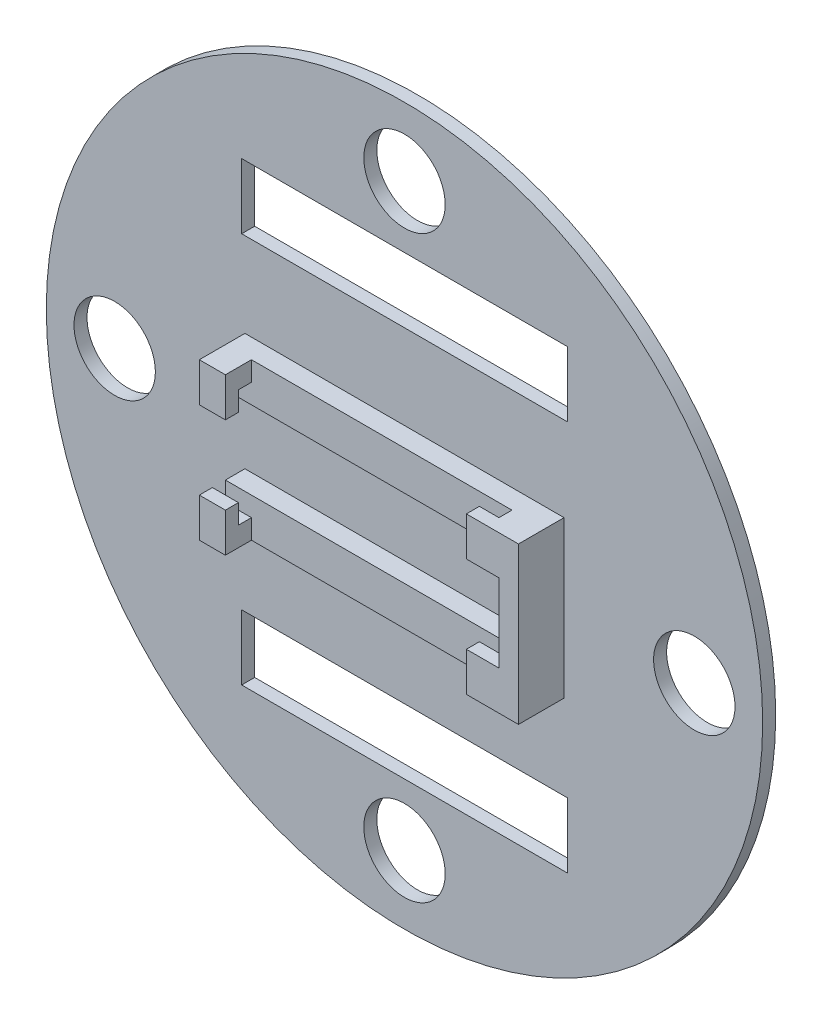
SolidWorks part; units mm, degrees
ref_plane "Front Plane" through (0, 0, 0) normal (0, 0, 1) x (1, 0, 0)
ref_plane "Top Plane" through (0, 0, 0) normal (0, 1, 0) x (1, 0, 0)
ref_plane "Right Plane" through (0, 0, 0) normal (1, 0, 0) x (0, 0, -1)
sketch "Sketch4" plane through (0, 0, 0) normal (0, 0, 1) x (1, 0, 0)
  circle A0 centre (0, 0) radius 59
  dimension "D1" = 118
extrude "Boss-Extrude3" add sketch "Sketch4" along normal blind 2
sketch "Sketch5" plane through (0, 0, 2) normal (0, 0, 1) x (1, 0, 0)
  line L1 (-22.5, 27.5) -> (22.5, 27.5)
  line L2 (-22.5, 27.5) -> (-22.5, -27.5)
  line L3 (-22.5, -27.5) -> (22.5, -27.5)
  line L4 (22.5, 27.5) -> (22.5, -27.5)
  circle A0 centre (0, 0) radius 59 construction
  circle A1 centre (-22.5, 27.5) radius 1.375
  circle A2 centre (22.5, 27.5) radius 1.375
  circle A3 centre (22.5, -27.5) radius 1.375
  circle A4 centre (-22.5, -27.5) radius 1.375
  dimension "D5" = 2.75
  dimension "D6" = 2.75
  dimension "D7" = 2.75
  dimension "D8" = 2.75
  dimension "D1" = 45
  dimension "D2" = 55
  dimension "D3" = 27.5
  dimension "D4" = 22.5
extrude "Boss-Extrude5" add sketch "Sketch5" along normal blind 7 contours A4 | A3 | A2 | A1
sketch "Sketch8" plane through (0, 0, 2) normal (0, 0, 1) x (1, 0, 0)
  circle A4 centre (-22.5, 27.5) radius 2.375
  circle A5 centre (-22.5, 27.5) radius 2.375
  circle A7 centre (22.5, 27.5) radius 2.375
  circle A8 centre (22.5, 27.5) radius 2.375
  circle A10 centre (-22.5, -27.5) radius 2.375
  circle A11 centre (-22.5, -27.5) radius 2.375
  circle A13 centre (22.5, -27.5) radius 2.375
  circle A14 centre (22.5, -27.5) radius 2.375
  dimension "D1" = 1
  dimension "D2" = 1
  dimension "D3" = 1
  dimension "D4" = 1
extrude "Boss-Extrude6" add sketch "Sketch8" along normal blind 2
sketch "Sketch9" plane through (0, 0, 2) normal (0, 0, 1) x (1, 0, 0)
  line L0 (4.7458, 55.7985) -> (5, 58.7878)
  line L1 (55.7985, -4.7458) -> (58.7878, -5)
  line L2 (-4.7458, 55.7985) -> (-5, 58.7878)
  line L3 (55.7985, 4.7458) -> (58.7878, 5)
  line L4 (-4.7458, -55.7985) -> (-5, -58.7878)
  line L5 (4.7458, -55.7985) -> (5, -58.7878)
  line L6 (-55.7985, 4.7458) -> (-58.7878, 5)
  line L7 (-55.7985, -4.7458) -> (-58.7878, -5)
  arc A0 (5, 58.7878) -> (-5, 58.7878) centre (0, 0) ccw
  arc A1 (5, 58.7878) -> (-5, 58.7878) centre (0, 0) ccw
  arc A2 (4.7458, 55.7985) -> (-4.7458, 55.7985) centre (0, 0) ccw
  arc A3 (55.7985, -4.7458) -> (55.7985, 4.7458) centre (0, 0) ccw
  arc A4 (58.7878, -5) -> (58.7878, 5) centre (0, 0) ccw
  arc A5 (-4.7458, -55.7985) -> (4.7458, -55.7985) centre (0, 0) ccw
  arc A6 (-5, -58.7878) -> (5, -58.7878) centre (0, 0) ccw
  arc A7 (-55.7985, 4.7458) -> (-55.7985, -4.7458) centre (0, 0) ccw
  arc A8 (-58.7878, 5) -> (-58.7878, -5) centre (0, 0) ccw
  point P25 (0, 0)
  circle M7 centre (0, 0) radius 59
  dimension "D1" = 118
  dimension "D2" = 3
  dimension "D3" = 4
extrude "Boss-Extrude7" add sketch "Sketch9" along normal blind 18 contours A2 L0 L2 M7 | A7 L6 L7 M7 | A4 L3 A3 L1 | A5 L5 A6 L4
sketch "Sketch10" plane through (0, 0, 2) normal (0, 0, 1) x (1, 0, 0)
  circle A0 centre (-40, 0) radius 7.5
  dimension "D1" = 15
  dimension "D2" = 40
extrude "Cut-Extrude1" cut sketch "Sketch10" against normal blind 18 contours A0
sketch "Sketch12" plane through (0, 0, 20) normal (0, 0, 1) x (1, 0, 0)
  circle A0 centre (0, 0) radius 57.5
  arc A1 (4.7458, 55.7985) -> (-4.7458, 55.7985) centre (0, 0) ccw construction
  dimension "D1" = 1.5
extrude "Cut-Extrude2" cut sketch "Sketch12" against normal blind 5
sketch "Sketch13" plane through (0, 0, 0) normal (0, 0, -1) x (-1, 0, 0)
  line L0 (-58.6183, 6.9928) -> (-53.5993, 6.5659)
  line L1 (-53.5993, -6.5659) -> (-58.6183, -6.9928)
  line L2 (6.9928, 58.6183) -> (6.5659, 53.5993)
  line L3 (-6.5659, 53.5993) -> (-6.9928, 58.6183)
  line L4 (58.6183, -6.9928) -> (53.5993, -6.5659)
  line L5 (53.5993, 6.5659) -> (58.6183, 6.9928)
  line L6 (-6.9928, -58.6183) -> (-6.5659, -53.5993)
  line L7 (6.5659, -53.5993) -> (6.9928, -58.6183)
  line L8 (5, 58.7878) -> (4.7458, 55.7985) construction
  line L9 (-4.7458, 55.7985) -> (-5, 58.7878) construction
  line L10 (55.7985, 4.7458) -> (58.7878, 5) construction
  line L11 (58.7878, -5) -> (55.7985, -4.7458) construction
  line L12 (4.7458, -55.7985) -> (5, -58.7878) construction
  line L13 (-5, -58.7878) -> (-4.7458, -55.7985) construction
  line L14 (-55.7985, -4.7458) -> (-58.7878, -5) construction
  line L15 (-58.7878, 5) -> (-55.7985, 4.7458) construction
  line L16 (4.7458, -55.7985) -> (5, -58.7878)
  line L17 (-5, -58.7878) -> (-4.7458, -55.7985)
  line L18 (-55.7985, -4.7458) -> (-58.7878, -5)
  line L19 (-58.7878, 5) -> (-55.7985, 4.7458)
  line L20 (-4.7458, 55.7985) -> (-5, 58.7878)
  line L21 (5, 58.7878) -> (4.7458, 55.7985)
  line L22 (55.7985, 4.7458) -> (58.7878, 5)
  line L23 (58.7878, -5) -> (55.7985, -4.7458)
  line L24 (4.8686, -57.2433) -> (5, -58.7878)
  line L25 (-5, -58.7878) -> (-4.8686, -57.2433)
  line L26 (-57.2433, -4.8686) -> (-58.7878, -5)
  line L27 (-58.7878, 5) -> (-57.2433, 4.8686)
  line L28 (-4.8686, 57.2433) -> (-5, 58.7878)
  line L29 (5, 58.7878) -> (4.8686, 57.2433)
  line L30 (57.2433, 4.8686) -> (58.7878, 5)
  line L31 (58.7878, -5) -> (57.2433, -4.8686)
  arc A0 (4.8686, 57.2433) -> (-4.8686, 57.2433) centre (0, 0) ccw
  circle A1 centre (0, 0) radius 59
  arc A2 (58.7878, -5) -> (58.7878, 5) centre (0, 0) ccw
  arc A3 (57.2433, -4.8686) -> (57.2433, 4.8686) centre (0, 0) ccw
  arc A4 (-4.8686, -57.2433) -> (4.8686, -57.2433) centre (0, 0) ccw
  arc A5 (-53.5993, 6.5659) -> (-53.5993, -6.5659) centre (0, 0) ccw
  arc A6 (6.5659, 53.5993) -> (-6.5659, 53.5993) centre (0, 0) ccw
  arc A7 (53.5993, -6.5659) -> (53.5993, 6.5659) centre (0, 0) ccw
  arc A8 (-6.5659, -53.5993) -> (6.5659, -53.5993) centre (0, 0) ccw
  circle A9 centre (0, 0) radius 59
  arc A10 (-5, -58.7878) -> (5, -58.7878) centre (0, 0) ccw
  arc A11 (-58.7878, 5) -> (-58.7878, -5) centre (0, 0) ccw
  arc A13 (-57.2433, 4.8686) -> (-57.2433, -4.8686) centre (0, 0) ccw
  arc A18 (5, -58.7878) -> (58.7878, -5) centre (0, 0) ccw
  arc A19 (-4.7458, -55.7985) -> (4.7458, -55.7985) centre (0, 0) ccw
  arc A20 (-58.7878, -5) -> (-5, -58.7878) centre (0, 0) ccw
  arc A21 (-55.7985, 4.7458) -> (-55.7985, -4.7458) centre (0, 0) ccw
  arc A22 (-5, 58.7878) -> (-58.7878, 5) centre (0, 0) ccw
  arc A23 (4.7458, 55.7985) -> (-4.7458, 55.7985) centre (0, 0) ccw
  arc A24 (58.7878, 5) -> (5, 58.7878) centre (0, 0) ccw
  arc A25 (55.7985, -4.7458) -> (55.7985, 4.7458) centre (0, 0) ccw
  arc A34 (4.7458, 55.7985) -> (-4.7458, 55.7985) centre (0, 0) ccw construction
  arc A35 (55.7985, -4.7458) -> (55.7985, 4.7458) centre (0, 0) ccw construction
  arc A36 (-4.7458, -55.7985) -> (4.7458, -55.7985) centre (0, 0) ccw construction
  arc A37 (-55.7985, 4.7458) -> (-55.7985, -4.7458) centre (0, 0) ccw construction
  dimension "D1" = 0
  dimension "D2" = 0
  dimension "D4" = 2
  dimension "D5" = 2
extrude "Cut-Extrude3" cut sketch "Sketch13" against normal blind 5.5
sketch "Sketch14" plane through (0, 0, 2) normal (0, 0, 1) x (1, 0, 0)
  circle A0 centre (0, 0) radius 44.4281
extrude "Cut-Extrude4" cut sketch "Sketch14" along normal blind 32
sketch "Sketch15" plane through (0, 0, 2) normal (0, 0, 1) x (1, 0, 0)
  line L2 (21.5, -6) -> (21.5, 6)
  line L6 (-24.5, -12) -> (24.5, -12)
  line L7 (24.5, -12) -> (24.5, 12)
  line L8 (-24.5, 12) -> (24.5, 12)
  line L9 (-24.5, -12) -> (-24.5, -6)
  line L10 (-24.5, 6) -> (-24.5, 12)
  line L11 (-24.5, 12) -> (24.5, 12)
  line L12 (-24.5, 12) -> (-24.5, 6)
  line L13 (-24.5, 6) -> (21.5, 6)
  line L14 (24.5, 12) -> (24.5, 6)
  line L15 (24.5, -12) -> (-24.5, -12)
  line L16 (24.5, -12) -> (24.5, -6)
  line L17 (21.5, -6) -> (-24.5, -6)
  line L18 (-24.5, -12) -> (-24.5, -6)
  line L19 (-24.5, -12) -> (-24.5, 12) construction
  line L21 (-21.5, -9) -> (-21.5, 9) construction
  line L24 (21.5, -9) -> (21.5, 9) construction
  line L25 (-21.5, 9) -> (21.5, 9) construction
  line L26 (-21.5, -9) -> (21.5, -9) construction
  point P1 (0, 0)
  dimension "D4" = 6
  dimension "D5" = 6
  dimension "D3" = 3
extrude "Boss-Extrude8" add sketch "Sketch15" along normal blind 3 contours L2 L17 L9 L6 L7 L8 L10 L13
sketch "Sketch17" plane through (0, 0, 5) normal (0, 0, 1) x (1, 0, 0)
  line L1 (21.5, -9) -> (-21.5, -9)
  line L2 (21.5, -9) -> (21.5, 9)
  line L3 (21.5, 9) -> (-21.5, 9)
  line L14 (-21.5, 9) -> (-24.5, 9)
  line L15 (-24.5, 12) -> (24.5, 12)
  line L16 (-24.5, 12) -> (-24.5, 9)
  line L17 (-24.5, -12) -> (24.5, -12)
  line L18 (24.5, 12) -> (24.5, -12)
  line L19 (-21.5, -9) -> (-24.5, -9)
  line L20 (-24.5, -9) -> (-24.5, -12)
  point P0 (0, 0)
  dimension "D1" = 43
  dimension "D2" = 18
extrude "Boss-Extrude9" add sketch "Sketch17" along normal blind 2
sketch "Sketch18" plane through (0, 0, 7) normal (0, 0, 1) x (1, 0, 0)
  line L0 (24.5, 12) -> (-24.5, 12) construction
  line L1 (-20.5, 12) -> (19.5, 12)
  line L2 (-20.5, 12) -> (-20.5, -12)
  line L3 (-20.5, -12) -> (19.5, -12)
  line L4 (19.5, 12) -> (19.5, -12)
  line L5 (-24.5, -12) -> (24.5, -12) construction
  line L6 (-24.5, 12) -> (-24.5, 9) construction
  dimension "D1" = 4
  dimension "D2" = 5
extrude "Cut-Extrude5" cut sketch "Sketch18" against normal blind 2
sketch "Sketch19" plane through (0, 0, 7) normal (0, 0, 1) x (1, 0, 0)
  line L0 (-24.5, 6) -> (21.5, 6) construction
  line L1 (-24.5, 12) -> (-20.5, 12)
  line L2 (-24.5, 12) -> (-24.5, 6)
  line L3 (-24.5, 6) -> (-20.5, 6)
  line L4 (-20.5, 12) -> (-20.5, 6)
  line L5 (21.5, -6) -> (-24.5, -6) construction
  line L6 (-24.5, -12) -> (-20.5, -12)
  line L7 (-24.5, -12) -> (-24.5, -6)
  line L8 (-24.5, -6) -> (-20.5, -6)
  line L9 (-20.5, -12) -> (-20.5, -6)
  line L10 (19.5, 12) -> (-20.5, 12) construction
  line L11 (24.5, -12) -> (16.5, -12)
  line L12 (24.5, -12) -> (24.5, 12)
  line L13 (24.5, 12) -> (16.5, 12)
  line L14 (16.5, -12) -> (16.5, 12)
  dimension "D1" = 4
  dimension "D2" = 4
  dimension "D3" = 8
extrude "Boss-Extrude10" add sketch "Sketch19" along normal blind 2
sketch "Sketch20" plane through (0, 0, 2) normal (0, 0, 1) x (1, 0, 0)
  circle A0 centre (0, 0) radius 50.9724
  circle A1 centre (0, 0) radius 71.0344
extrude "Cut-Extrude6" cut sketch "Sketch20" along normal blind 57
sketch "Sketch21" plane through (0, 0, 2) normal (0, 0, 1) x (1, 0, 0)
  circle A0 centre (0, 0) radius 57
  circle A1 centre (0, 0) radius 79.1442
  dimension "D1" = 114
extrude "Cut-Extrude8" cut sketch "Sketch21" against normal blind 57
sketch "Sketch23" plane through (0, 0, 2) normal (0, 0, 1) x (1, 0, 0)
  line L0 (0, 57) -> (0, 64.4029) construction
  line L1 (-5, 57) -> (5, 57)
  line L2 (4.6313, 52.7973) -> (5, 57)
  line L3 (-4.6313, 52.7973) -> (-5, 57)
  line L4 (52.7973, 4.6313) -> (57, 5)
  line L5 (57, 5) -> (57, -5)
  line L6 (52.7973, -4.6313) -> (57, -5)
  line L7 (4.6313, -52.7973) -> (5, -57)
  line L8 (5, -57) -> (-5, -57)
  line L9 (-4.6313, -52.7973) -> (-5, -57)
  line L10 (-52.7973, -4.6313) -> (-57, -5)
  line L11 (-57, -5) -> (-57, 5)
  line L12 (-52.7973, 4.6313) -> (-57, 5)
  circle A0 centre (0, 0) radius 57
  arc A1 (4.6313, 52.7973) -> (-4.6313, 52.7973) centre (0, 0) ccw
  circle A2 centre (0, 0) radius 57
  arc A3 (52.7973, -4.6313) -> (52.7973, 4.6313) centre (0, 0) ccw
  circle A4 centre (0, 0) radius 57
  arc A5 (-4.6313, -52.7973) -> (4.6313, -52.7973) centre (0, 0) ccw
  circle A6 centre (0, 0) radius 57
  arc A7 (-52.7973, 4.6313) -> (-52.7973, -4.6313) centre (0, 0) ccw
  point P8 (0, 57)
  point P28 (0, 0)
  circle M19 centre (0, 0) radius 57
  dimension "D1" = 114
  dimension "D2" = 4
  dimension "D3" = 10
  dimension "D4" = 4
extrude "Boss-Extrude11" add sketch "Sketch23" along normal blind 22 contours A1 L2 L3 M19 | A3 L6 L4 M19 | A7 L10 L11 L12 | A5 L7 L8 L9
sketch "Sketch24" plane through (0, 0, 24) normal (0, 0, 1) x (1, 0, 0)
  circle A0 centre (0, 0) radius 57
  circle A1 centre (0, 0) radius 89.5881
  dimension "D1" = 114
extrude "Cut-Extrude12" cut sketch "Sketch24" against normal blind 75
sketch "Sketch25" plane through (0, 0, 2) normal (0, 0, 1) x (1, 0, 0)
  circle A0 centre (0, 0) radius 55
  circle A1 centre (0, 0) radius 63.0853
  dimension "D1" = 110
extrude "Cut-Extrude13" cut sketch "Sketch25" against normal blind 10
sketch "Sketch26" plane through (0, 0, 0) normal (0, 0, -1) x (-1, 0, 0)
  circle A0 centre (0, 0) radius 55
  circle A1 centre (0, 0) radius 62.7158
extrude "Cut-Extrude14" cut sketch "Sketch26" against normal blind 43
sketch "Sketch27" plane through (0, 0, 24) normal (0, 0, 1) x (1, 0, 0)
  circle A0 centre (-55, 0) radius 8.6287
  arc A1 (-54.7896, 4.8061) -> (-54.7896, -4.8061) centre (0, 0) ccw construction
  circle A2 centre (0, -55) radius 7.7712
  arc A3 (-4.8061, -54.7896) -> (4.8061, -54.7896) centre (0, 0) ccw construction
  circle A4 centre (55, 0) radius 11.5322
  arc A5 (54.7896, -4.8061) -> (54.7896, 4.8061) centre (0, 0) ccw construction
  circle A6 centre (0, 53) radius 7.0527
  arc A7 (4.6313, 52.7973) -> (-4.6313, 52.7973) centre (0, 0) ccw construction
extrude "Cut-Extrude15" cut sketch "Sketch27" against normal up to surface (22 mm away) up to face at (-0.75, 0, 2)
sketch "Sketch28" plane through (0, 0, 2) normal (0, 0, 1) x (1, 0, 0)
  circle A0 centre (0, 0) radius 55
extrude "Boss-Extrude12" add sketch "Sketch28" against normal up to surface (2 mm away) up to face at (-32.5, 0, 0)
sketch "Sketch29" plane through (0, 0, 9) normal (0, 0, 1) x (1, 0, 0)
  line L0 (16.5, 12) -> (16.5, -12) construction
  line L1 (21.5, 6) -> (16.5, 6)
  line L2 (21.5, 6) -> (21.5, -6)
  line L3 (21.5, -6) -> (16.5, -6)
  line L4 (16.5, 6) -> (16.5, -6)
  line L5 (21.5, -6) -> (-24.5, -6) construction
extrude "Cut-Extrude16" cut sketch "Sketch29" against normal blind 3
sketch "Sketch30" plane through (0, 0, 2) normal (0, 0, 1) x (1, 0, 0)
  line L0 (0, 55) -> (0, -55) construction
  line L1 (55, 0) -> (-55, 0) construction
  circle A0 centre (0, 0) radius 55 construction
  circle A1 centre (0, 0) radius 44.5
  circle A2 centre (0, 44.5) radius 6.25
  circle A3 centre (44.5, 0) radius 6.25
  circle A4 centre (0, -44.5) radius 6.25
  circle A5 centre (-44.5, 0) radius 6.25
  dimension "D1" = 10.5
  dimension "D2" = 12.5
  dimension "D3" = 12.5
  dimension "D4" = 12.5
  dimension "D5" = 12.5
extrude "Cut-Extrude17" cut sketch "Sketch30" against normal blind 3 contours A2 | A3 | A4 | A5
sketch "Sketch31" plane through (0, 0, 2) normal (0, 0, 1) x (1, 0, 0)
  line L1 (-25, 35) -> (25, 35)
  line L2 (-25, 35) -> (-25, 25)
  line L3 (-25, 25) -> (25, 25)
  line L4 (25, 35) -> (25, 25)
  line L5 (25, -35) -> (-25, -35)
  line L6 (25, -35) -> (25, -25)
  line L7 (25, -25) -> (-25, -25)
  line L8 (-25, -35) -> (-25, -25)
  circle A0 centre (0, 0) radius 55 construction
  dimension "D1" = 50
  dimension "D2" = 50
  dimension "D3" = 10
  dimension "D4" = 10
  dimension "D5" = 25
  dimension "D6" = 25
  dimension "D7" = 25
  dimension "D8" = 25
extrude "Cut-Extrude18" cut sketch "Sketch31" against normal blind 3
